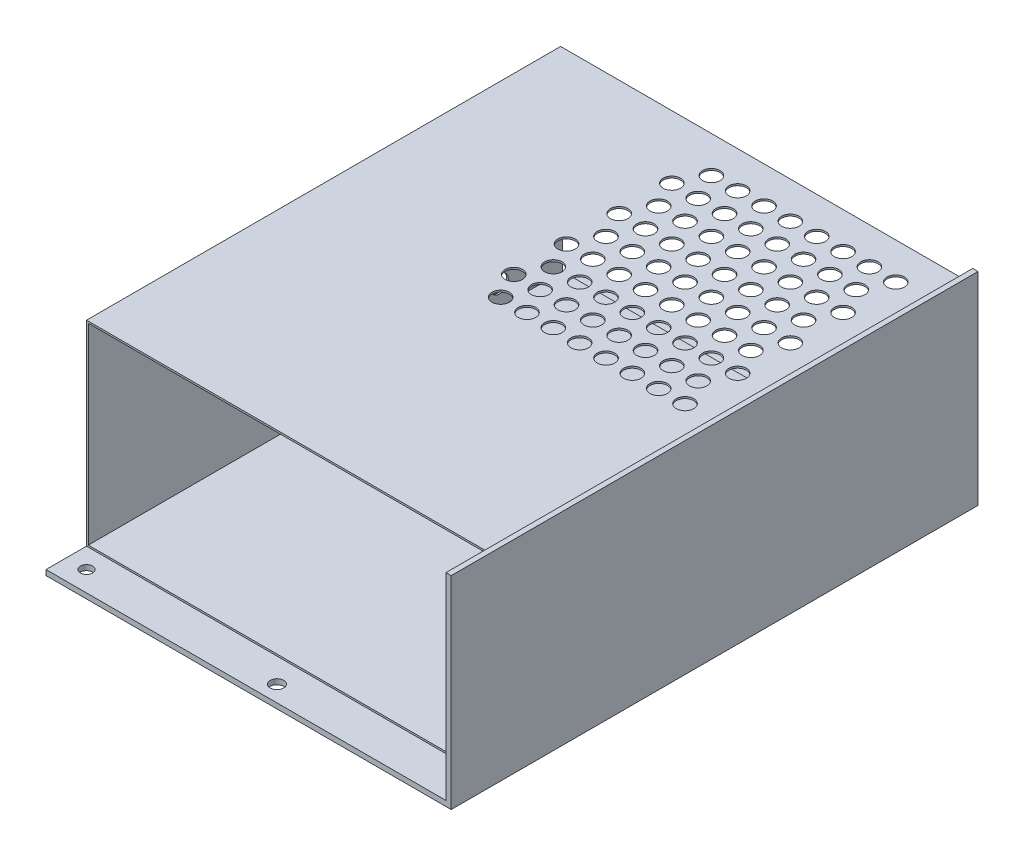
SolidWorks part; units mm, degrees
ref_plane "Front Plane" through (0, 0, 0) normal (0, 0, 1) x (1, 0, 0)
ref_plane "Top Plane" through (0, 0, 0) normal (0, 1, 0) x (1, 0, 0)
ref_plane "Right Plane" through (0, 0, 0) normal (1, 0, 0) x (0, 0, -1)
sketch "Sketch1" plane through (0, 0, 0) normal (0, 1, 0) x (1, 0, 0)
  line L1 (-50, -65) -> (50, -65)
  line L2 (-50, -65) -> (-50, 65)
  line L3 (-50, 65) -> (50, 65)
  line L4 (50, -65) -> (50, 65)
  line L5 (-50, -65) -> (50, 65) construction
  line L6 (-50, 65) -> (50, -65) construction
  point P0 (0, 0)
  dimension "D1" = 130
  dimension "D2" = 100
extrude "Boss-Extrude1" add sketch "Sketch1" along normal blind 1.3
sketch "Sketch2" plane through (0, 1.3, 0) normal (0, 1, 0) x (1, 0, 0)
  line L0 (-50, -65) -> (50, -65) construction
  line L1 (50, 65) -> (48.7, 65)
  line L2 (50, 65) -> (50, -65)
  line L3 (50, -65) -> (48.7, -65)
  line L4 (48.7, 65) -> (48.7, -65)
  dimension "D1" = 1.3
extrude "Boss-Extrude2" add sketch "Sketch2" along normal blind 48.7
sketch "Sketch3" plane through (0, 1.3, 0) normal (0, 1, 0) x (1, 0, 0)
  line L2 (-50, 65) -> (-50, -65) construction
  line L3 (-50, -65) -> (48.7, -65) construction
  circle A0 centre (-45, -60) radius 1.5
  circle A1 centre (-45, 7) radius 1.5
  circle A2 centre (3, -61) radius 1.65
  dimension "D1" = 5
  dimension "D2" = 5
  dimension "D3" = 3
  dimension "D5" = 67
  dimension "D6" = 3.3
  dimension "D7" = 4
  dimension "D8" = 48
  dimension "D4" = 2
extrude "Cut-Extrude1" cut sketch "Sketch3" against normal up to next
sketch "Sketch4" plane through (0, 1.3, 0) normal (0, 1, 0) x (1, 0, 0)
  line L0 (48.7, 65) -> (48.7, -65) construction
  line L1 (48.7, 62) -> (-50, 62)
  line L2 (48.7, 62) -> (48.7, -55)
  line L3 (48.7, -55) -> (-50, -55)
  line L4 (-50, 62) -> (-50, -55)
  line L5 (-50, 65) -> (-50, -65) construction
  line L6 (48.7, 65) -> (-50, 65) construction
  line L7 (-50, -65) -> (48.7, -65) construction
  dimension "D1" = 3
  dimension "D2" = 10
extrude "Boss-Extrude3" add sketch "Sketch4" along normal blind 48.3 separate body
shell "Shell1" thickness 0.44
sketch "Sketch5" plane through (0, 49.6, 0) normal (0, 1, 0) x (1, 0, 0)
  line L0 (48.7, 62) -> (-50, 62) construction
  line L1 (48.7, 65) -> (48.7, -65) construction
  circle A0 centre (41.7, 53) radius 2.15
  circle A1 centre (38.45, 46.5) radius 2.15
  circle A2 centre (35.2, 53) radius 2.15
  circle A3 centre (31.95, 46.5) radius 2.15
  circle A4 centre (28.7, 53) radius 2.15
  circle A5 centre (25.45, 46.5) radius 2.15
  circle A6 centre (22.2, 53) radius 2.15
  circle A7 centre (18.95, 46.5) radius 2.15
  circle A8 centre (15.7, 53) radius 2.15
  circle A9 centre (12.45, 46.5) radius 2.15
  circle A10 centre (9.2, 53) radius 2.15
  circle A11 centre (5.95, 46.5) radius 2.15
  circle A12 centre (2.7, 53) radius 2.15
  circle A13 centre (-0.55, 46.5) radius 2.15
  circle A14 centre (-3.8, 53) radius 2.15
  circle A15 centre (-7.05, 46.5) radius 2.15
  circle A16 centre (41.7, 40) radius 2.15
  circle A17 centre (38.45, 33.5) radius 2.15
  circle A18 centre (35.2, 40) radius 2.15
  circle A19 centre (31.95, 33.5) radius 2.15
  circle A20 centre (28.7, 40) radius 2.15
  circle A21 centre (25.45, 33.5) radius 2.15
  circle A22 centre (22.2, 40) radius 2.15
  circle A23 centre (18.95, 33.5) radius 2.15
  circle A24 centre (15.7, 40) radius 2.15
  circle A25 centre (12.45, 33.5) radius 2.15
  circle A26 centre (9.2, 40) radius 2.15
  circle A27 centre (5.95, 33.5) radius 2.15
  circle A28 centre (2.7, 40) radius 2.15
  circle A29 centre (-0.55, 33.5) radius 2.15
  circle A30 centre (-3.8, 40) radius 2.15
  circle A31 centre (-7.05, 33.5) radius 2.15
  circle A32 centre (41.7, 27) radius 2.15
  circle A33 centre (38.45, 20.5) radius 2.15
  circle A34 centre (35.2, 27) radius 2.15
  circle A35 centre (31.95, 20.5) radius 2.15
  circle A36 centre (28.7, 27) radius 2.15
  circle A37 centre (25.45, 20.5) radius 2.15
  circle A38 centre (22.2, 27) radius 2.15
  circle A39 centre (18.95, 20.5) radius 2.15
  circle A40 centre (15.7, 27) radius 2.15
  circle A41 centre (12.45, 20.5) radius 2.15
  circle A42 centre (9.2, 27) radius 2.15
  circle A43 centre (5.95, 20.5) radius 2.15
  circle A44 centre (2.7, 27) radius 2.15
  circle A45 centre (-0.55, 20.5) radius 2.15
  circle A46 centre (-3.8, 27) radius 2.15
  circle A47 centre (-7.05, 20.5) radius 2.15
  circle A48 centre (41.7, 14) radius 2.15
  circle A49 centre (38.45, 7.5) radius 2.15
  circle A50 centre (35.2, 14) radius 2.15
  circle A51 centre (31.95, 7.5) radius 2.15
  circle A52 centre (28.7, 14) radius 2.15
  circle A53 centre (25.45, 7.5) radius 2.15
  circle A54 centre (22.2, 14) radius 2.15
  circle A55 centre (18.95, 7.5) radius 2.15
  circle A56 centre (15.7, 14) radius 2.15
  circle A57 centre (12.45, 7.5) radius 2.15
  circle A58 centre (9.2, 14) radius 2.15
  circle A59 centre (5.95, 7.5) radius 2.15
  circle A60 centre (2.7, 14) radius 2.15
  circle A61 centre (-0.55, 7.5) radius 2.15
  circle A62 centre (-3.8, 14) radius 2.15
  circle A63 centre (-7.05, 7.5) radius 2.15
  circle A64 centre (41.7, 1) radius 2.15
  circle A65 centre (35.2, 1) radius 2.15
  circle A66 centre (28.7, 1) radius 2.15
  circle A67 centre (22.2, 1) radius 2.15
  circle A68 centre (15.7, 1) radius 2.15
  circle A69 centre (9.2, 1) radius 2.15
  circle A70 centre (2.7, 1) radius 2.15
  circle A71 centre (-3.8, 1) radius 2.15
  dimension "D1" = 9
  dimension "D2" = 4.3
  dimension "D3" = 7
  dimension "D4" = 4.3
  dimension "D5" = 6.5
  dimension "D6" = 3.25
  dimension "D8" = 6.5
  dimension "D10" = 6.5
  dimension "D12" = 6.5
  dimension "D7" = 8
  dimension "D9" = 4
  dimension "D11" = 2
extrude "Cut-Extrude2" cut sketch "Sketch5" against normal up to surface (0.44 mm away) up to face at (-0.65, 49.16, -3.5)
sketch "Sketch6" plane through (-50, 0, 0) normal (-1, 0, 0) x (0, 0, 1)
  line L0 (-46.5, 49.6) -> (-46.5, 1.3) construction
  line L1 (-44.35, 49.6) -> (-48.65, 49.6) construction
  line L2 (-65, 1.3) -> (65, 1.3) construction
  circle A0 centre (-46.5, 6.8) radius 2.15
  circle A1 centre (-40, 10.05) radius 2.15
  circle A2 centre (-33.5, 6.8) radius 2.15
  circle A3 centre (-27, 10.05) radius 2.15
  circle A4 centre (-20.5, 6.8) radius 2.15
  circle A5 centre (-14, 10.05) radius 2.15
  circle A6 centre (-7.5, 6.8) radius 2.15
  circle A7 centre (-1, 10.05) radius 2.15
  circle A8 centre (-33.5, 13.3) radius 2.15
  circle A9 centre (-27, 16.55) radius 2.15
  circle A10 centre (-20.5, 13.3) radius 2.15
  circle A11 centre (-14, 16.55) radius 2.15
  circle A12 centre (-7.5, 13.3) radius 2.15
  circle A13 centre (-1, 16.55) radius 2.15
  circle A14 centre (-33.5, 19.8) radius 2.15
  circle A15 centre (-27, 23.05) radius 2.15
  circle A16 centre (-20.5, 19.8) radius 2.15
  circle A17 centre (-14, 23.05) radius 2.15
  circle A18 centre (-7.5, 19.8) radius 2.15
  circle A19 centre (-1, 23.05) radius 2.15
  circle A20 centre (-33.5, 26.3) radius 2.15
  circle A21 centre (-27, 29.55) radius 2.15
  circle A22 centre (-20.5, 26.3) radius 2.15
  circle A23 centre (-14, 29.55) radius 2.15
  circle A24 centre (-7.5, 26.3) radius 2.15
  circle A25 centre (-1, 29.55) radius 2.15
  circle A26 centre (-33.5, 32.8) radius 2.15
  circle A27 centre (-27, 36.05) radius 2.15
  circle A28 centre (-20.5, 32.8) radius 2.15
  circle A29 centre (-14, 36.05) radius 2.15
  circle A30 centre (-7.5, 32.8) radius 2.15
  circle A31 centre (-1, 36.05) radius 2.15
  circle A32 centre (-46.5, 13.3) radius 2.15
  circle A33 centre (-40, 16.55) radius 2.15
  circle A34 centre (-46.5, 19.8) radius 2.15
  circle A35 centre (-40, 23.05) radius 2.15
  circle A36 centre (-46.5, 26.3) radius 2.15
  circle A37 centre (-40, 29.55) radius 2.15
  circle A38 centre (-46.5, 32.8) radius 2.15
  circle A39 centre (-40, 36.05) radius 2.15
  dimension "D1" = 4.3
  dimension "D2" = 5.5
  dimension "D3" = 4.3
  dimension "D4" = 3.25
  dimension "D5" = 6.5
  dimension "D8" = 6.5
  dimension "D9" = 13
  dimension "D10" = 9.75
  dimension "D6" = 4
  dimension "D7" = 5
extrude "Cut-Extrude3" cut sketch "Sketch6" against normal up to surface (0.44 mm away) up to face at (-49.56, 25.45, -3.5)
